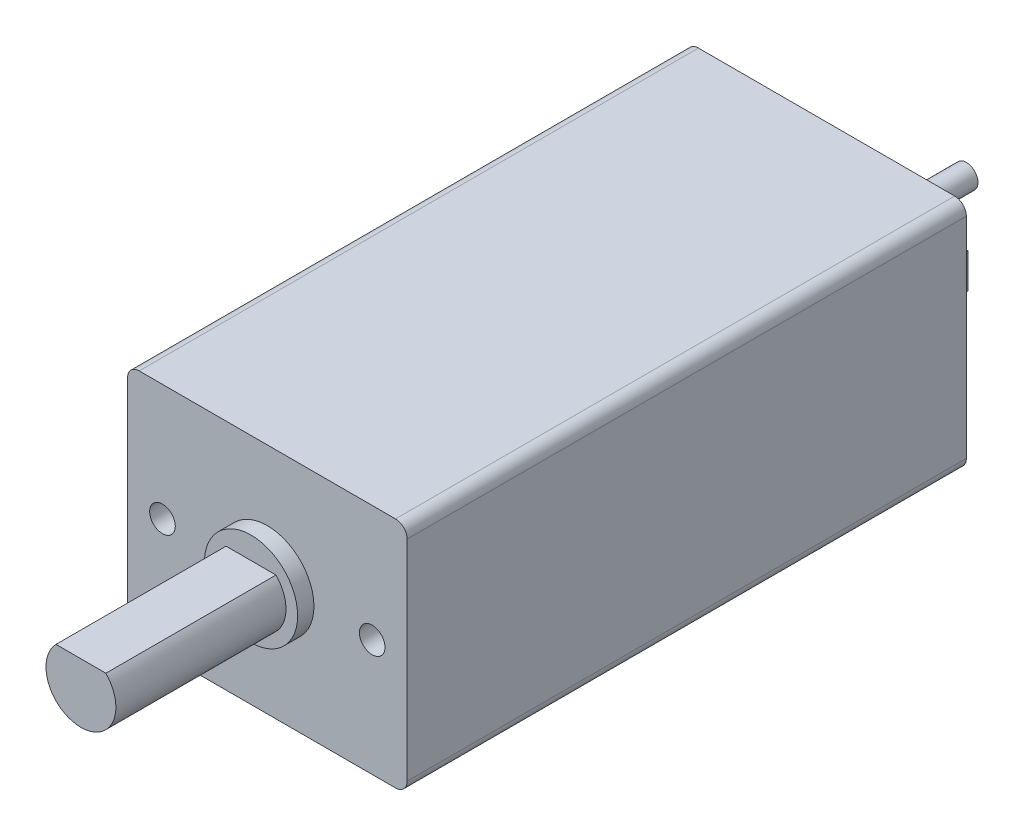
SolidWorks part; units mm, degrees
ref_plane "Ebene vorne" through (0, 0, 0) normal (0, 0, 1) x (1, 0, 0)
ref_plane "Ebene oben" through (0, 0, 0) normal (0, 1, 0) x (1, 0, 0)
ref_plane "Ebene rechts" through (0, 0, 0) normal (1, 0, 0) x (0, 0, -1)
sketch "top" plane through (0, 0, 0) normal (0, 0, 1) x (1, 0, 0)
  line L0 (-6, 5) -> (6, -5) construction
  line L1 (-6, 5) -> (6, 5)
  line L2 (-6, 5) -> (-6, -5)
  line L3 (-6, -5) -> (6, -5)
  line L4 (6, 5) -> (6, -5)
  line L5 (6, 5) -> (-6, -5) construction
  point P4 (0, 0)
  dimension "D1" = 10
  dimension "D2" = 12
extrude "Precision Microdrives Model 212-109" add sketch "top" against normal blind 24
sketch "top ring" plane through (0, 0, 0) normal (0, 0, 1) x (1, 0, 0)
  circle A0 centre (0, 0) radius 2
  dimension "D1" = 4
extrude "top-ring" add sketch "top ring" along normal blind 0.7
hole_wizard "M1-1" positions "Skizze6" profile "Skizze5" hole size "M1" standard "ISO"
sketch "Skizze6" plane through (0, 0, 0) normal (0, 0, 1) x (1, 0, 0)
  line L0 (-6, 0) -> (6, 0) construction
  line L1 (-6, 5) -> (-6, -5) construction
  line L2 (6, -5) -> (6, 5) construction
  point P0 (-4.5, 0)
  dimension "D1" = 4.5
sketch "Skizze5" plane through (-4.5, 0, 0) normal (1, 0, 0) x (0, -1, 0)
  line L0 (0, 0) -> (0, 10.337)
  line L1 (0, 10.337) -> (0.55, 10)
  line L2 (0.55, 10) -> (0.55, 0)
  line L5 (0.55, 0) -> (0, 0)
  line L10 (0, 10.337) -> (-0.55, 10) construction
  line L11 (0, -6.35) -> (0, 107.95) construction
  dimension "Bohrerdurchmesser" = 1.1
  dimension "Bohrungstiefe" = 10
  dimension "Spitzenwinkel" = 117
hole_wizard "M1-2" positions "Skizze8" profile "Skizze7" hole size "M1" standard "ISO"
sketch "Skizze8" plane through (0, 0, 0) normal (0, 0, 1) x (1, 0, 0)
  line L0 (-6, 0) -> (6, 0) construction
  line L1 (-6, 5) -> (-6, -5) construction
  line L2 (6, -5) -> (6, 5) construction
  point P0 (4.5, 0)
  dimension "D1" = 4.5
sketch "Skizze7" plane through (4.5, 0, 0) normal (1, 0, 0) x (0, -1, 0)
  line L0 (0, 0) -> (0, 10.337)
  line L1 (0, 10.337) -> (0.55, 10)
  line L2 (0.55, 10) -> (0.55, 0)
  line L5 (0.55, 0) -> (0, 0)
  line L10 (0, 10.337) -> (-0.55, 10) construction
  line L11 (0, -6.35) -> (0, 107.95) construction
  dimension "Bohrerdurchmesser" = 1.1
  dimension "Bohrungstiefe" = 10
  dimension "Spitzenwinkel" = 117
sketch "Skizze11" plane through (0, 0, 0) normal (0, 0, 1) x (1, 0, 0)
  line L1 (0, 1.05) -> (1.0712, 1.05) construction
  line L2 (0, 1.05) -> (-1.0712, 1.05) construction
  line L3 (-1.0712, 1.05) -> (1.0712, 1.05)
  arc A1 (-1.0712, 1.05) -> (1.0712, 1.05) centre (0, 0) ccw
extrude "D-Shaft" add sketch "Skizze11" along normal blind 8
fillet "Verrundung1" radius 0.5 4 edges at (-6, 5, -12) (6, 5, -12) (6, -5, -12) (-6, -5, -12)
sketch "Skizze12" plane through (0, 0, -24) normal (0, 0, -1) x (-1, 0, 0)
  circle A0 centre (0, 0) radius 2.5
  dimension "D1" = 5
extrude "bottom" add sketch "Skizze12" along normal blind 1.2
sketch "Skizze13" plane through (0, 0, -24) normal (0, 0, -1) x (-1, 0, 0)
  circle A0 centre (0, 0) radius 0.5
  dimension "D1" = 1
extrude "bolt" add sketch "Skizze13" along normal blind 6
sketch "Skizze14" plane through (0, 0, -24) normal (0, 0, -1) x (-1, 0, 0)
  line L0 (-6, 0) -> (6, 0) construction
  line L1 (-6, -4.5) -> (-6, 4.5) construction
  line L2 (6, 4.5) -> (6, -4.5) construction
  line L4 (-3.56, 0.75) -> (-3.44, 0.75)
  line L5 (-3.56, 0.75) -> (-3.56, -0.75)
  line L6 (-3.56, -0.75) -> (-3.44, -0.75)
  line L7 (-3.44, 0.75) -> (-3.44, -0.75)
  line L8 (-3.56, 0.75) -> (-3.44, -0.75) construction
  line L9 (-3.56, -0.75) -> (-3.44, 0.75) construction
  line L10 (3.44, 0.75) -> (3.56, 0.75)
  line L11 (3.44, 0.75) -> (3.44, -0.75)
  line L12 (3.44, -0.75) -> (3.56, -0.75)
  line L13 (3.56, 0.75) -> (3.56, -0.75)
  line L14 (3.44, 0.75) -> (3.56, -0.75) construction
  line L15 (3.44, -0.75) -> (3.56, 0.75) construction
  point P6 (-3.5, 0)
  point P11 (3.5, 0)
  dimension "D1" = 1.5
  dimension "D2" = 0.12
  dimension "D3" = 1.5
  dimension "D4" = 0.12
  dimension "D5" = 3.5
  dimension "D6" = 3.5
extrude "flaps" add sketch "Skizze14" along normal blind 2.5
sketch "Skizze15" plane through (-3.56, 0, 0) normal (-1, 0, 0) x (0, 0, 1)
  line L0 (-26.5, -0.75) -> (-26.5, 0.75) construction
  circle A0 centre (-25.7, 0) radius 0.4
  point P2 (-26.5, 0)
  dimension "D1" = 0.8
  dimension "D2" = 0.8
extrude "flap1-cut" cut sketch "Skizze15" against normal up to next
sketch "Skizze16" plane through (3.56, 0, 0) normal (1, 0, 0) x (0, 0, -1)
  line L0 (26.5, 0.75) -> (26.5, -0.75) construction
  circle A0 centre (25.7, 0) radius 0.4
  dimension "D1" = 0.8
  dimension "D2" = 0.8
extrude "flap2-cut" cut sketch "Skizze16" against normal up to next
sketch "Skizze17" plane through (0, 0, 0) normal (0, 0, 1) x (1, 0, 0)
  line L0 (0, 5) -> (0, -5) construction
  line L1 (5.5, 5) -> (-5.5, 5) construction
  line L2 (-5.5, -5) -> (5.5, -5) construction
  line L3 (-6, 0) -> (6, 0) construction
  line L4 (-6, 4.5) -> (-6, -4.5) construction
  line L5 (6, -4.5) -> (6, 4.5) construction
